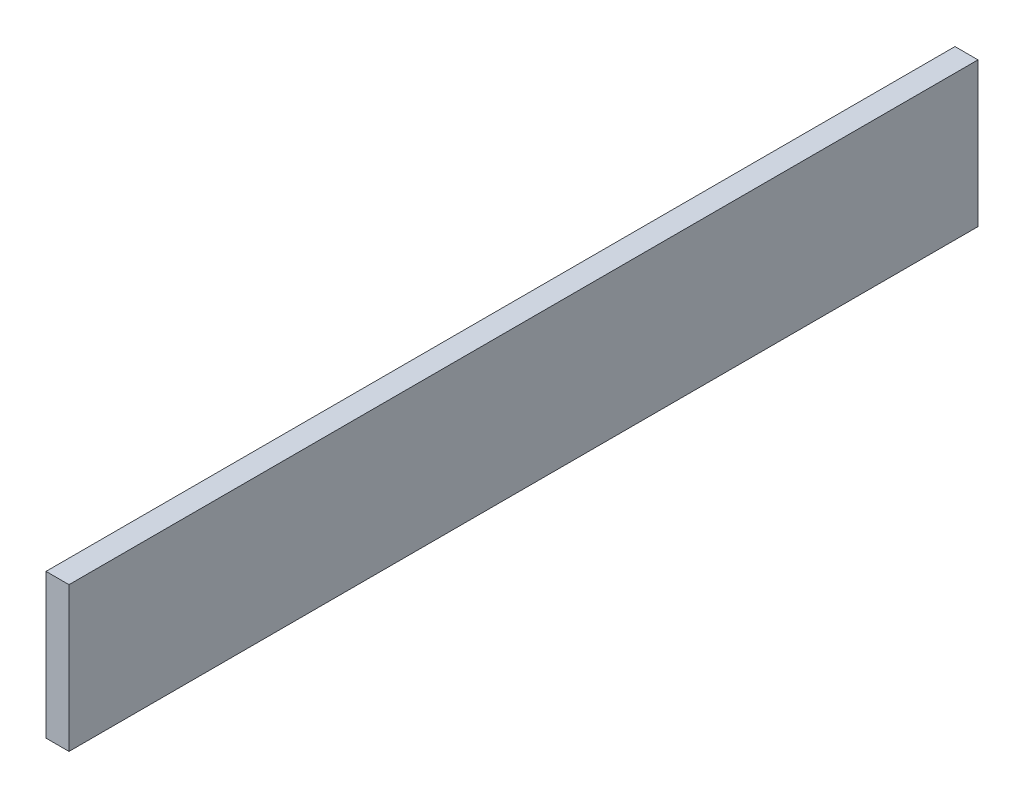
SolidWorks part; units mm, degrees
material "6061-T6 (SS)"
ref_plane "Front" through (0, 0, 0) normal (0, 0, 1) x (1, 0, 0)
ref_plane "Top" through (0, 0, 0) normal (0, 1, 0) x (1, 0, 0)
ref_plane "Right" through (0, 0, 0) normal (1, 0, 0) x (0, 0, -1)
sketch "Sketch1" plane through (0, 0, 0) normal (1, 0, 0) x (0, 0, -1)
  line L1 (-125.476, -19.939) -> (125.476, -19.939)
  line L2 (-125.476, -19.939) -> (-125.476, 19.939)
  line L3 (-125.476, 19.939) -> (125.476, 19.939)
  line L4 (125.476, -19.939) -> (125.476, 19.939)
  line L5 (-125.476, -19.939) -> (125.476, 19.939) construction
  line L6 (-125.476, 19.939) -> (125.476, -19.939) construction
  point P0 (0, 0)
  dimension "D1" = 39.878
  dimension "D2" = 250.952
extrude "Boss-Extrude1" add sketch "Sketch1" along normal blind 6.35
